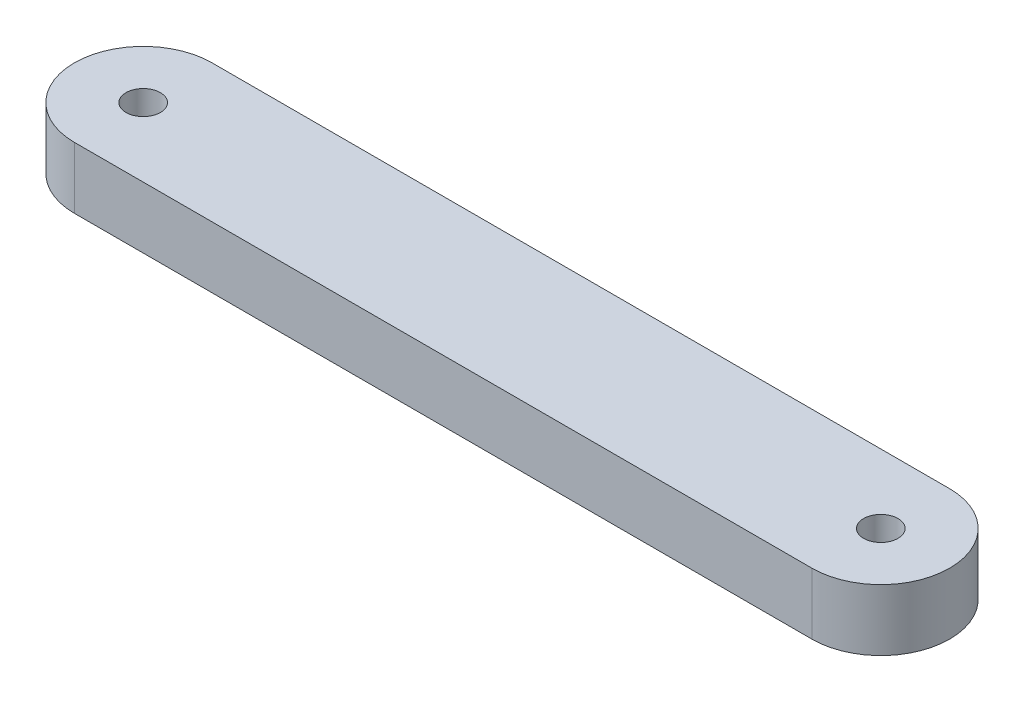
SolidWorks part; units mm, degrees
ref_plane "前视基准面" through (0, 0, 0) normal (0, 0, 1) x (1, 0, 0)
ref_plane "上视基准面" through (0, 0, 0) normal (0, 1, 0) x (1, 0, 0)
ref_plane "右视基准面" through (0, 0, 0) normal (1, 0, 0) x (0, 0, -1)
sketch "草图1" plane through (0, 0, 0) normal (0, 1, 0) x (1, 0, 0)
  line L0 (-259.2308, 0) -> (242.3077, 0) construction
  line L1 (0, 184.2308) -> (0, -188.8462) construction
  line L2 (-150, 28) -> (150, 28)
  line L5 (150, -28) -> (-150, -28)
  circle A0 centre (-150, 0) radius 7
  circle A1 centre (-150, 0) radius 28
  circle A2 centre (150, 0) radius 7
  circle A3 centre (150, 0) radius 28
  dimension "D2" = 14
  dimension "D3" = 56
  dimension "D1" = 150
extrude "凸台-拉伸1" add sketch "草图1" along normal blind 25 contours L5 A3 L2 A1 | A3 A2 | A1 A0
